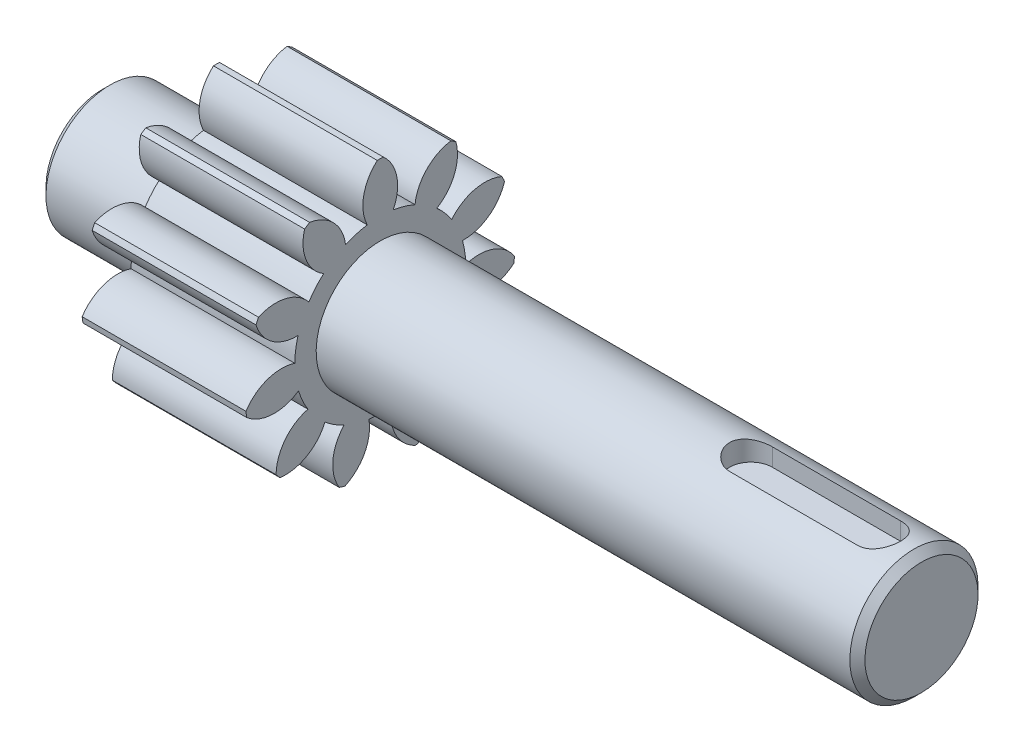
SolidWorks part; units mm, degrees
ref_plane "Front Plane" through (0, 0, 0) normal (0, 0, 1) x (1, 0, 0)
ref_plane "Top Plane" through (0, 0, 0) normal (0, 1, 0) x (1, 0, 0)
ref_plane "Right Plane" through (0, 0, 0) normal (1, 0, 0) x (0, 0, -1)
sketch "Sketch1" plane through (0, 0, 0) normal (0, 0, 1) x (1, 0, 0)
  line L0 (-100, 0) -> (100, 0) construction
  line L1 (-57.5, 0) -> (-57.5, -7.9393)
  line L2 (-56.4393, -9) -> (56.4393, -9)
  line L3 (57.5, -7.9393) -> (57.5, 0)
  line L4 (-57.5, -7.9393) -> (-56.4393, -9)
  line L5 (-57.5, 0) -> (57.5, 0)
  line L6 (57.5, -7.9393) -> (56.4393, -9)
  point P5 (0, 0)
  dimension "D1" = 200
  dimension "D4" = 1.5
  dimension "D5" = 45
revolve "Revolve1" add sketch "Sketch1" angle 360 about L0
ref_plane "Plane1" through (-41.5, 0, 0) normal (-1, 0, 0) x (0, 0, 1)
sketch "Sketch2" plane through (-41.5, 0, 0) normal (-1, 0, 0) x (0, 0, 1)
  arc A0 (-1.825, 11.8604) -> (-4.8769, 10.9643) centre (0, 0) ccw
  arc A1 (-1.825, 11.8604) -> (-0.42, 18.9954) centre (3.5604, 14.5057) cw
  arc A2 (1.825, 11.8604) -> (0.42, 18.9954) centre (-3.5604, 14.5057) ccw
  arc A3 (0.42, 18.9954) -> (-0.42, 18.9954) centre (0, 0) ccw
  arc A4 (4.8769, 10.9643) -> (1.825, 11.8604) centre (0, 0) ccw
  arc A5 (7.9475, 8.9909) -> (10.623, 15.7528) centre (4.8472, 14.1279) ccw
  arc A6 (10.623, 15.7528) -> (9.9163, 16.207) centre (0, 0) ccw
  arc A7 (4.8769, 10.9643) -> (9.9163, 16.207) centre (10.8376, 10.2781) cw
  arc A8 (10.0305, 6.5871) -> (7.9475, 8.9909) centre (0, 0) ccw
  arc A9 (11.5467, 3.2669) -> (17.4533, 7.5089) centre (11.7159, 9.2645) ccw
  arc A10 (17.4533, 7.5089) -> (17.1043, 8.273) centre (0, 0) ccw
  arc A11 (10.0305, 6.5871) -> (17.1043, 8.273) centre (14.6739, 2.7873) cw
  arc A12 (11.9994, 0.1185) -> (11.5467, 3.2669) centre (0, 0) ccw
  arc A13 (11.48, -3.4943) -> (18.7422, -3.119) centre (14.8648, 1.4597) ccw
  arc A14 (18.7422, -3.119) -> (18.8618, -2.2876) centre (0, 0) ccw
  arc A15 (11.9994, 0.1185) -> (18.8618, -2.2876) centre (13.8514, -5.5885) cw
  arc A16 (10.1586, -6.3877) -> (11.48, -3.4943) centre (0, 0) ccw
  arc A17 (7.7684, -9.1462) -> (14.0807, -12.7567) centre (13.2943, -6.8085) ccw
  arc A18 (14.0807, -12.7567) -> (14.6308, -12.1219) centre (0, 0) ccw
  arc A19 (10.1586, -6.3877) -> (14.6308, -12.1219) centre (8.6312, -12.19) cw
  arc A20 (5.0925, -10.8658) -> (7.7684, -9.1462) centre (0, 0) ccw
  arc A21 (1.5904, -11.8941) -> (4.9486, -18.3442) centre (7.5029, -12.9151) ccw
  arc A22 (4.9486, -18.3442) -> (5.7546, -18.1076) centre (0, 0) ccw
  arc A23 (5.0925, -10.8658) -> (5.7546, -18.1076) centre (0.6706, -14.9212) cw
  arc A24 (-1.5904, -11.8941) -> (1.5904, -11.8941) centre (0, 0) ccw
  arc A25 (-5.0925, -10.8658) -> (-5.7546, -18.1076) centre (-0.6706, -14.9212) ccw
  arc A26 (-5.7546, -18.1076) -> (-4.9486, -18.3442) centre (0, 0) ccw
  arc A27 (-1.5904, -11.8941) -> (-4.9486, -18.3442) centre (-7.5029, -12.9151) cw
  arc A28 (-7.7684, -9.1462) -> (-5.0925, -10.8658) centre (0, 0) ccw
  arc A29 (-10.1586, -6.3877) -> (-14.6308, -12.1219) centre (-8.6312, -12.19) ccw
  arc A30 (-14.6308, -12.1219) -> (-14.0807, -12.7567) centre (0, 0) ccw
  arc A31 (-7.7684, -9.1462) -> (-14.0807, -12.7567) centre (-13.2943, -6.8085) cw
  arc A32 (-11.48, -3.4943) -> (-10.1586, -6.3877) centre (0, 0) ccw
  arc A33 (-11.9994, 0.1185) -> (-18.8618, -2.2876) centre (-13.8514, -5.5885) ccw
  arc A34 (-18.8618, -2.2876) -> (-18.7422, -3.119) centre (0, 0) ccw
  arc A35 (-11.48, -3.4943) -> (-18.7422, -3.119) centre (-14.8648, 1.4597) cw
  arc A36 (-11.5467, 3.2669) -> (-11.9994, 0.1185) centre (0, 0) ccw
  arc A37 (-10.0305, 6.5871) -> (-17.1043, 8.273) centre (-14.6739, 2.7873) ccw
  arc A38 (-17.1043, 8.273) -> (-17.4533, 7.5089) centre (0, 0) ccw
  arc A39 (-11.5467, 3.2669) -> (-17.4533, 7.5089) centre (-11.7159, 9.2645) cw
  arc A40 (-7.9475, 8.9909) -> (-10.0305, 6.5871) centre (0, 0) ccw
  arc A41 (-4.8769, 10.9643) -> (-9.9163, 16.207) centre (-10.8376, 10.2781) ccw
  arc A42 (-9.9163, 16.207) -> (-10.623, 15.7528) centre (0, 0) ccw
  arc A43 (-7.9475, 8.9909) -> (-10.623, 15.7528) centre (-4.8472, 14.1279) cw
  arc A44 (-7.9475, 8.9909) -> (-10.0305, 6.5871) centre (0, 0) ccw
  arc A45 (-1.825, 11.8604) -> (-4.8769, 10.9643) centre (0, 0) ccw
  arc A46 (-1.825, 11.8604) -> (-4.8769, 10.9643) centre (0, 0) ccw
  arc A47 (4.8769, 10.9643) -> (1.825, 11.8604) centre (0, 0) ccw
  arc A48 (4.8769, 10.9643) -> (1.825, 11.8604) centre (0, 0) ccw
  arc A49 (4.8769, 10.9643) -> (1.825, 11.8604) centre (0, 0) ccw
  arc A50 (4.8769, 10.9643) -> (1.825, 11.8604) centre (0, 0) ccw
  arc A51 (4.8769, 10.9643) -> (1.825, 11.8604) centre (0, 0) ccw
  arc A52 (4.8769, 10.9643) -> (1.825, 11.8604) centre (0, 0) ccw
  arc A53 (4.8769, 10.9643) -> (1.825, 11.8604) centre (0, 0) ccw
  arc A54 (4.8769, 10.9643) -> (1.825, 11.8604) centre (0, 0) ccw
  arc A55 (4.8769, 10.9643) -> (1.825, 11.8604) centre (0, 0) ccw
  arc A56 (4.8769, 10.9643) -> (1.825, 11.8604) centre (0, 0) ccw
  arc A57 (10.0305, 6.5871) -> (7.9475, 8.9909) centre (0, 0) ccw
  arc A58 (10.0305, 6.5871) -> (7.9475, 8.9909) centre (0, 0) ccw
  arc A59 (10.0305, 6.5871) -> (7.9475, 8.9909) centre (0, 0) ccw
  arc A60 (10.0305, 6.5871) -> (7.9475, 8.9909) centre (0, 0) ccw
  arc A61 (10.0305, 6.5871) -> (7.9475, 8.9909) centre (0, 0) ccw
  arc A62 (10.0305, 6.5871) -> (7.9475, 8.9909) centre (0, 0) ccw
  arc A63 (10.0305, 6.5871) -> (7.9475, 8.9909) centre (0, 0) ccw
  arc A64 (10.0305, 6.5871) -> (7.9475, 8.9909) centre (0, 0) ccw
  arc A65 (10.0305, 6.5871) -> (7.9475, 8.9909) centre (0, 0) ccw
  arc A66 (10.0305, 6.5871) -> (7.9475, 8.9909) centre (0, 0) ccw
  arc A67 (11.9994, 0.1185) -> (11.5467, 3.2669) centre (0, 0) ccw
  arc A68 (11.9994, 0.1185) -> (11.5467, 3.2669) centre (0, 0) ccw
  arc A69 (11.9994, 0.1185) -> (11.5467, 3.2669) centre (0, 0) ccw
  arc A70 (11.9994, 0.1185) -> (11.5467, 3.2669) centre (0, 0) ccw
  arc A71 (11.9994, 0.1185) -> (11.5467, 3.2669) centre (0, 0) ccw
  arc A72 (11.9994, 0.1185) -> (11.5467, 3.2669) centre (0, 0) ccw
  arc A73 (11.9994, 0.1185) -> (11.5467, 3.2669) centre (0, 0) ccw
  arc A74 (11.9994, 0.1185) -> (11.5467, 3.2669) centre (0, 0) ccw
  arc A75 (11.9994, 0.1185) -> (11.5467, 3.2669) centre (0, 0) ccw
  arc A76 (11.9994, 0.1185) -> (11.5467, 3.2669) centre (0, 0) ccw
  arc A77 (10.1586, -6.3877) -> (11.48, -3.4943) centre (0, 0) ccw
  arc A78 (10.1586, -6.3877) -> (11.48, -3.4943) centre (0, 0) ccw
  arc A79 (10.1586, -6.3877) -> (11.48, -3.4943) centre (0, 0) ccw
  arc A80 (10.1586, -6.3877) -> (11.48, -3.4943) centre (0, 0) ccw
  arc A81 (10.1586, -6.3877) -> (11.48, -3.4943) centre (0, 0) ccw
  arc A82 (10.1586, -6.3877) -> (11.48, -3.4943) centre (0, 0) ccw
  arc A83 (10.1586, -6.3877) -> (11.48, -3.4943) centre (0, 0) ccw
  arc A84 (10.1586, -6.3877) -> (11.48, -3.4943) centre (0, 0) ccw
  arc A85 (10.1586, -6.3877) -> (11.48, -3.4943) centre (0, 0) ccw
  arc A86 (10.1586, -6.3877) -> (11.48, -3.4943) centre (0, 0) ccw
  arc A87 (5.0925, -10.8658) -> (7.7684, -9.1462) centre (0, 0) ccw
  arc A88 (5.0925, -10.8658) -> (7.7684, -9.1462) centre (0, 0) ccw
  arc A89 (5.0925, -10.8658) -> (7.7684, -9.1462) centre (0, 0) ccw
  arc A90 (5.0925, -10.8658) -> (7.7684, -9.1462) centre (0, 0) ccw
  arc A91 (5.0925, -10.8658) -> (7.7684, -9.1462) centre (0, 0) ccw
  arc A92 (5.0925, -10.8658) -> (7.7684, -9.1462) centre (0, 0) ccw
  arc A93 (5.0925, -10.8658) -> (7.7684, -9.1462) centre (0, 0) ccw
  arc A94 (5.0925, -10.8658) -> (7.7684, -9.1462) centre (0, 0) ccw
  arc A95 (5.0925, -10.8658) -> (7.7684, -9.1462) centre (0, 0) ccw
  arc A96 (5.0925, -10.8658) -> (7.7684, -9.1462) centre (0, 0) ccw
  arc A97 (-1.5904, -11.8941) -> (1.5904, -11.8941) centre (0, 0) ccw
  arc A98 (-1.5904, -11.8941) -> (1.5904, -11.8941) centre (0, 0) ccw
  arc A99 (-1.5904, -11.8941) -> (1.5904, -11.8941) centre (0, 0) ccw
  arc A100 (-1.5904, -11.8941) -> (1.5904, -11.8941) centre (0, 0) ccw
  arc A101 (-1.5904, -11.8941) -> (1.5904, -11.8941) centre (0, 0) ccw
  arc A102 (-1.5904, -11.8941) -> (1.5904, -11.8941) centre (0, 0) ccw
  arc A103 (-1.5904, -11.8941) -> (1.5904, -11.8941) centre (0, 0) ccw
  arc A104 (-1.5904, -11.8941) -> (1.5904, -11.8941) centre (0, 0) ccw
  arc A105 (-1.5904, -11.8941) -> (1.5904, -11.8941) centre (0, 0) ccw
  arc A106 (-1.5904, -11.8941) -> (1.5904, -11.8941) centre (0, 0) ccw
  arc A107 (-7.7684, -9.1462) -> (-5.0925, -10.8658) centre (0, 0) ccw
  arc A108 (-7.7684, -9.1462) -> (-5.0925, -10.8658) centre (0, 0) ccw
  arc A109 (-7.7684, -9.1462) -> (-5.0925, -10.8658) centre (0, 0) ccw
  arc A110 (-7.7684, -9.1462) -> (-5.0925, -10.8658) centre (0, 0) ccw
  arc A111 (-7.7684, -9.1462) -> (-5.0925, -10.8658) centre (0, 0) ccw
  arc A112 (-7.7684, -9.1462) -> (-5.0925, -10.8658) centre (0, 0) ccw
  arc A113 (-7.7684, -9.1462) -> (-5.0925, -10.8658) centre (0, 0) ccw
  arc A114 (-7.7684, -9.1462) -> (-5.0925, -10.8658) centre (0, 0) ccw
  arc A115 (-7.7684, -9.1462) -> (-5.0925, -10.8658) centre (0, 0) ccw
  arc A116 (-7.7684, -9.1462) -> (-5.0925, -10.8658) centre (0, 0) ccw
  arc A117 (-11.48, -3.4943) -> (-10.1586, -6.3877) centre (0, 0) ccw
  arc A118 (-11.48, -3.4943) -> (-10.1586, -6.3877) centre (0, 0) ccw
  arc A119 (-11.48, -3.4943) -> (-10.1586, -6.3877) centre (0, 0) ccw
  arc A120 (-11.48, -3.4943) -> (-10.1586, -6.3877) centre (0, 0) ccw
  arc A121 (-11.48, -3.4943) -> (-10.1586, -6.3877) centre (0, 0) ccw
  arc A122 (-11.48, -3.4943) -> (-10.1586, -6.3877) centre (0, 0) ccw
  arc A123 (-11.48, -3.4943) -> (-10.1586, -6.3877) centre (0, 0) ccw
  arc A124 (-11.48, -3.4943) -> (-10.1586, -6.3877) centre (0, 0) ccw
  arc A125 (-11.48, -3.4943) -> (-10.1586, -6.3877) centre (0, 0) ccw
  arc A126 (-11.48, -3.4943) -> (-10.1586, -6.3877) centre (0, 0) ccw
  arc A127 (-7.9475, 8.9909) -> (-10.0305, 6.5871) centre (0, 0) ccw
  arc A128 (-7.9475, 8.9909) -> (-10.0305, 6.5871) centre (0, 0) ccw
  arc A129 (-7.9475, 8.9909) -> (-10.0305, 6.5871) centre (0, 0) ccw
  arc A130 (-7.9475, 8.9909) -> (-10.0305, 6.5871) centre (0, 0) ccw
  arc A131 (-7.9475, 8.9909) -> (-10.0305, 6.5871) centre (0, 0) ccw
  arc A132 (-7.9475, 8.9909) -> (-10.0305, 6.5871) centre (0, 0) ccw
  arc A133 (-7.9475, 8.9909) -> (-10.0305, 6.5871) centre (0, 0) ccw
  arc A134 (-7.9475, 8.9909) -> (-10.0305, 6.5871) centre (0, 0) ccw
  arc A135 (-7.9475, 8.9909) -> (-10.0305, 6.5871) centre (0, 0) ccw
  arc A136 (-1.825, 11.8604) -> (-4.8769, 10.9643) centre (0, 0) ccw
  arc A137 (-1.825, 11.8604) -> (-4.8769, 10.9643) centre (0, 0) ccw
  arc A138 (-1.825, 11.8604) -> (-4.8769, 10.9643) centre (0, 0) ccw
  arc A139 (-1.825, 11.8604) -> (-4.8769, 10.9643) centre (0, 0) ccw
  arc A140 (-1.825, 11.8604) -> (-4.8769, 10.9643) centre (0, 0) ccw
  arc A141 (-1.825, 11.8604) -> (-4.8769, 10.9643) centre (0, 0) ccw
  arc A142 (-1.825, 11.8604) -> (-4.8769, 10.9643) centre (0, 0) ccw
  arc A143 (-1.825, 11.8604) -> (-4.8769, 10.9643) centre (0, 0) ccw
  arc A144 (-11.5467, 3.2669) -> (-11.9994, 0.1185) centre (0, 0) ccw
  arc A145 (-11.5467, 3.2669) -> (-11.9994, 0.1185) centre (0, 0) ccw
  arc A146 (-11.5467, 3.2669) -> (-11.9994, 0.1185) centre (0, 0) ccw
  arc A147 (-11.5467, 3.2669) -> (-11.9994, 0.1185) centre (0, 0) ccw
  arc A148 (-11.5467, 3.2669) -> (-11.9994, 0.1185) centre (0, 0) ccw
  arc A149 (-11.5467, 3.2669) -> (-11.9994, 0.1185) centre (0, 0) ccw
  arc A150 (-11.5467, 3.2669) -> (-11.9994, 0.1185) centre (0, 0) ccw
  arc A151 (-11.5467, 3.2669) -> (-11.9994, 0.1185) centre (0, 0) ccw
  arc A152 (-11.5467, 3.2669) -> (-11.9994, 0.1185) centre (0, 0) ccw
  arc A153 (-11.5467, 3.2669) -> (-11.9994, 0.1185) centre (0, 0) ccw
  point P6 (0, 0)
  point P74 (0, 0)
  dimension "D1" = 24
  dimension "D2" = 6
  dimension "D3" = 38
  dimension "D4" = 3.65
  dimension "D5" = 0.84
  dimension "D6" = 11
extrude "Boss-Extrude1" add sketch "Sketch2" against normal blind 23 contours A43 A40 A37 A38 A39 A36 A33 A34 A35 A32 A29 A30 A31 A28 A25 A26 A27 A24 A21 A22 A23 A20 A17 A18 A19 A16 A13 A14 A15 A12 A9 A10 A11 A8 A5 A6 A7 A4 A2 A3 A1 A0 A41 A42
ref_plane "Plane2" through (0, 9, 0) normal (0, 1, 0) x (1, 0, 0)
sketch "Sketch4" plane through (0, 9, 0) normal (0, 1, 0) x (1, 0, 0)
  line L2 (33.55, 3) -> (51.55, 3)
  line L3 (33.55, -3) -> (51.55, -3)
  arc A0 (51.55, -3) -> (51.55, 3) centre (51.55, 0) ccw
  arc A1 (33.55, 3) -> (33.55, -3) centre (33.55, 0) ccw
  point P13 (0, 0)
  dimension "D1" = 6
  dimension "D2" = 6
  dimension "D3" = 18
extrude "Cut-Extrude1" cut sketch "Sketch4" against normal blind 3
